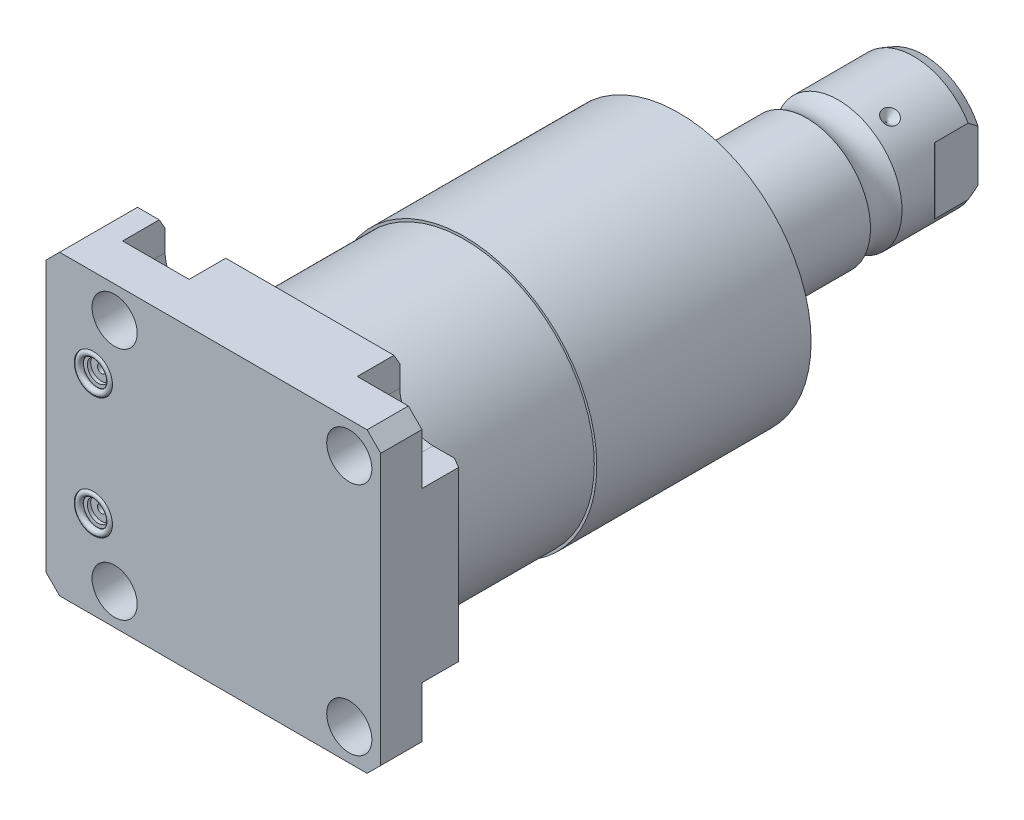
SolidWorks part; units mm, degrees
material "Alloy Steel"
ref_plane "Front Plane" through (0, 0, 0) normal (0, 0, 1) x (1, 0, 0)
ref_plane "Top Plane" through (0, 0, 0) normal (0, 1, 0) x (1, 0, 0)
ref_plane "Right Plane" through (0, 0, 0) normal (1, 0, 0) x (0, 0, -1)
sketch "Sketch1" plane through (0, 0, 0) normal (0, 0, 1) x (1, 0, 0)
  line L0 (-55.55, 44.45) -> (44.45, 44.45)
  line L1 (44.45, 44.45) -> (44.45, -44.45)
  line L2 (44.45, -44.45) -> (-55.55, -44.45)
  line L3 (-55.55, -44.45) -> (-55.55, 44.45)
  dimension "D1" = 100
  dimension "D2" = 88.9
  dimension "D3" = 44.45
  dimension "D4" = 44.45
extrude "Extrude1" add sketch "Sketch1" along normal blind 25.019
hole_wizard "Hole1" positions "Sketch22" profile "Sketch21" legacy end condition through all
sketch "Sketch22" plane through (0, 0, 0) normal (0, 0, -1) x (-1, 0, 0)
  line L0 (0, 0) -> (42.7441, 0) construction
  line L1 (0, 0.8532) -> (0, 27.5062) construction
  point P0 (-35.052, -35.052)
  point P9 (-35.052, 35.052)
  point P11 (35.052, 35.052)
  point P12 (35.052, -35.052)
  dimension "D1" = 35.052
  dimension "D2" = 35.052
sketch "Sketch21" plane through (35.052, -35.052, 0) normal (1, 0, 0) x (0, 1, 0)
  line L0 (0, 0) -> (0, 25.019)
  line L1 (0, 25.019) -> (6.7435, 25.019)
  line L2 (6.7435, 25.019) -> (6.7435, 0)
  line L3 (6.7435, 0) -> (0, 0)
  line L4 (0, 110) -> (0, -10) construction
  dimension "Diameter" = 13.487
  dimension "Depth" = 25.019
sketch "Sketch3" plane through (0, 0, 0) normal (0, 0, -1) x (-1, 0, 0)
  line L0 (-35.052, -25.1205) -> (-44.45, -25.1205)
  line L1 (-44.45, -44.45) -> (-44.45, -25.1205)
  line L2 (-44.45, 25.1205) -> (-44.45, 44.45)
  line L3 (-44.45, 25.1205) -> (-35.052, 25.1205)
  line L4 (-25.1205, 35.052) -> (-25.1205, 44.45)
  line L5 (-44.45, 44.45) -> (-25.1205, 44.45)
  line L6 (25.1205, 44.45) -> (25.1205, 35.052)
  line L7 (44.9835, 35.052) -> (44.9835, 44.45)
  line L8 (25.1205, 44.45) -> (44.9835, 44.45)
  line L9 (44.9835, -44.45) -> (25.1205, -44.45)
  line L10 (44.9835, -44.45) -> (44.9835, -35.052)
  line L11 (25.1205, -35.052) -> (25.1205, -44.45)
  line L12 (-25.1205, -44.45) -> (-44.45, -44.45)
  line L13 (-25.1205, -44.45) -> (-25.1205, -35.052)
  line L14 (-44.45, 44.45) -> (55.55, 44.45) construction
  line L15 (-44.45, -44.45) -> (-44.45, 44.45) construction
  line L16 (55.55, -44.45) -> (-44.45, -44.45) construction
  arc A0 (-25.1205, -35.052) -> (-35.052, -25.1205) centre (-35.052, -35.052) ccw
  arc A1 (-35.052, 25.1205) -> (-25.1205, 35.052) centre (-35.052, 35.052) ccw
  arc A2 (25.1205, 35.052) -> (44.9835, 35.052) centre (35.052, 35.052) ccw
  arc A3 (44.9835, -35.052) -> (25.1205, -35.052) centre (35.052, -35.052) ccw
  circle A8 centre (-35.052, 35.052) radius 6.7435 construction
  circle A9 centre (-35.052, -35.052) radius 6.7435 construction
  circle A10 centre (35.052, -35.052) radius 6.7435 construction
  circle A11 centre (35.052, 35.052) radius 6.7435 construction
  dimension "D1" = 9.9315
extrude "Cut-Extrude2" cut sketch "Sketch3" against normal blind 12.7
ref_plane "Plane16" through (0, 0, 12.014) normal (0, 0, 1) x (1, 0, 0)
sketch "Sketch23" plane through (0, 0, 12.014) normal (0, 0, 1) x (1, 0, 0)
  line L0 (-11.9397, -13.0048) -> (-61.0013, -13.0048) construction
  line L1 (-55.55, -23.749) -> (-55.296, -23.749)
  line L3 (-55.296, -23.749) -> (-55.296, -19.6596)
  line L4 (-55.296, -19.6596) -> (-54.5848, -18.9484)
  line L5 (-54.5848, -18.9484) -> (-41.1228, -18.9484)
  line L6 (-41.1228, -18.9484) -> (-41.1228, -13.0048)
  line L7 (-41.1228, -13.0048) -> (-55.55, -13.0048)
  line L8 (-55.55, -13.0048) -> (-55.55, -23.749)
  line L10 (-55.55, 44.45) -> (-55.55, -44.45) construction
  dimension "D1" = 21.4884
  dimension "D2" = 0.254
  dimension "D3" = 45
  dimension "D4" = 13.3096
  dimension "D5" = 11.8872
  dimension "D6" = 14.1732
  dimension "D7" = 13.0048
revolve "Cut-Revolve5" cut sketch "Sketch23" angle 360 about L0
mirror "Mirror1" about plane through (0, 0, 0) normal (0, 1, 0) of "Cut-Revolve5"
sketch "Sketch6" plane through (0, 0, 25.019) normal (0, 0, 1) x (1, 0, 0)
  line L0 (0, 0) -> (-71.0417, 0) construction
  circle A0 centre (-41.402, -18.11) radius 5.7023
  circle A1 centre (-41.402, 18.11) radius 5.7023
  dimension "D4" = 11.4046
  dimension "D1" = 18.11
  dimension "D2" = 36.22
  dimension "D3" = 41.402
extrude "Cut-Extrude3" cut sketch "Sketch6" against normal blind 1.4478
sketch "Sketch7" plane through (0, 0, 23.5712) normal (0, 0, 1) x (1, 0, 0)
  circle A0 centre (-41.402, 18.11) radius 3.2512
  circle A1 centre (-41.402, -18.11) radius 3.2512
  circle A2 centre (-41.402, 18.11) radius 5.7023 construction
  circle A3 centre (-41.402, -18.11) radius 5.7023 construction
  dimension "D1" = 6.5024
extrude "Cut-Extrude4" cut sketch "Sketch7" against normal blind 1.016
sketch "Sketch8" plane through (0, 0, 22.5552) normal (0, 0, 1) x (1, 0, 0)
  circle A0 centre (-41.402, 18.11) radius 1.2446
  circle A1 centre (-41.402, -18.11) radius 1.2446
  circle A2 centre (-41.402, 18.11) radius 5.7023 construction
  circle A3 centre (-41.402, -18.11) radius 5.7023 construction
  dimension "D1" = 2.4892
extrude "Cut-Extrude5" cut sketch "Sketch8" against normal blind 11.9888
ref_plane "Plane17" through (0, 18.11, 0) normal (0, 1, 0) x (-1, 0, 0)
sketch "Sketch9" plane through (-41.656, 18.11, 23.5712) normal (0, 1, 0) x (1, 0, 0)
  line L0 (0.254, -1.9469) -> (0.254, 0.0927) construction
  line L3 (-5.4483, 0) -> (5.9563, 0) construction
  line L4 (0.254, 13.0048) -> (0.254, 1.016) construction
  circle A0 centre (5.0292, -0.9271) radius 0.9271
  dimension "D1" = 1.8542
  dimension "D2" = 9.5504
revolve "Revolve1" add sketch "Sketch9" angle 360 about L0
mirror "Mirror2" about plane through (0, 0, 0) normal (0, 1, 0) of bodies 116
chamfer "Chamfer1" distance 4.064 angle 45 4 edges at (44.45, -44.45, 18.8595) (44.45, 44.45, 18.8595) (-55.55, 44.45, 12.5095) (-55.55, -44.45, 12.5095)
chamfer "Chamfer2" distance 3.0226 angle 30 5 edges at (-48.2347, -44.45, 0) (0, -44.45, 0) (44.45, 0, 0) (-48.2347, 44.45, 0) (0, 44.45, 0)
sketch "Sketch24" plane through (0, 0, 0) normal (1, 0, 0) x (0, 0, -1)
  line L0 (0, 0) -> (113.9127, 0) construction
  line L1 (0, 0) -> (0, 38.786)
  line L2 (0, 38.786) -> (44.45, 38.786)
  line L3 (44.45, 38.786) -> (44.45, 39.5225)
  line L4 (44.45, 39.5225) -> (108.4839, 39.5225)
  line L5 (108.4839, 39.5225) -> (112.268, 25.4)
  line L6 (112.268, 25.4) -> (112.268, 0)
  line L7 (112.268, 0) -> (0, 0)
  dimension "D1" = 77.572
  dimension "D2" = 44.45
  dimension "D3" = 79.045
  dimension "D4" = 50.8
  dimension "D5" = 15
  dimension "D6" = 112.268
revolve "Revolve4" add sketch "Sketch24" angle 360 about L0
sketch "Sketch17" plane through (0, 0, 0) normal (1, 0, 0) x (0, 0, -1)
  line L0 (112.268, 0) -> (112.268, -19.05)
  line L1 (112.268, -19.05) -> (146.7029, -19.05)
  line L2 (156.1171, -19.05) -> (178.664, -19.05)
  line L3 (181.585, -17.9868) -> (181.585, 0)
  line L4 (181.585, 0) -> (112.268, 0)
  line L5 (130.8989, 0) -> (0.816, 0) construction
  line L6 (112.268, -25.4) -> (112.268, 25.4) construction
  line L7 (-25.019, -40.386) -> (-25.019, 40.386) construction
  line L8 (181.585, -17.9868) -> (178.664, -19.05)
  arc A0 (156.1171, -19.05) -> (146.7029, -19.05) centre (151.41, -25.4254) ccw
  dimension "D2" = 20
  dimension "D4" = 7.9248
  dimension "D5" = 35.0012
  dimension "D1" = 206.604
  dimension "D3" = 38.1
  dimension "D6" = 30.175
  dimension "D7" = 2.921
revolve "Revolve3" add sketch "Sketch17" angle 360 about L5
sketch "Sketch28" plane through (0, 0, 0) normal (0, 1, 0) x (1, 0, 0)
  line L0 (-34.3062, 162.078) -> (35.4095, 162.078) construction
  line L1 (-19.05, 164.491) -> (-16.637, 162.078)
  line L2 (-19.05, 178.664) -> (-19.05, 156.1171) construction
  line L3 (-16.637, 162.078) -> (-19.05, 162.078)
  line L4 (-19.05, 162.078) -> (-19.05, 164.491)
  arc A0 (-19.05, 146.7029) -> (-19.05, 156.1171) centre (-25.4254, 151.41) ccw construction
  dimension "D3" = 10.668
  dimension "D1" = 45
  dimension "D2" = 4.826
revolve "Cut-Revolve6" cut sketch "Sketch28" angle 360 about L0
pattern_circular "CirPattern1" count 3 over 360 about axis through (0, 0, -130.8989) along (0, 0, -1) of "Cut-Revolve6"
hole_wizard "Hole2" positions "Sketch33" profile "Sketch32" legacy
sketch "Sketch33" plane through (0, 0, -181.585) normal (0, 0, -1) x (-1, 0, 0)
  circle A0 centre (0, 0) radius 19.05 construction
  point P0 (0, 0)
sketch "Sketch32" plane through (0, 0, -181.585) normal (1, 0, 0) x (0, 1, 0)
  line L0 (0, 0) -> (0, 29.5665)
  line L1 (0, 29.5665) -> (6.9342, 25.4)
  line L2 (6.9342, 25.4) -> (6.9342, 0)
  line L4 (6.9342, 0) -> (0, 0)
  line L6 (0, 29.5665) -> (-6.9342, 25.4) construction
  line L7 (0, -4.2442) -> (0, 117.3081) construction
  dimension "Diameter" = 13.8684
  dimension "Depth" = 25.4
  dimension "Drill Angle" = 118
sketch "Sketch34" plane through (0, 0, 0) normal (0, 1, 0) x (0, 0, -1)
  line L0 (0, 0) -> (211.3651, 0) construction
  line L1 (165.8009, 19.05) -> (168.3462, 16.5047)
  line L3 (168.885, 16.2815) -> (181.585, 16.2815)
  line L4 (181.585, -17.9868) -> (181.585, 17.9868) construction
  line L5 (181.585, 16.2815) -> (181.585, 19.05)
  line L6 (181.585, 19.05) -> (165.8009, 19.05)
  line L7 (181.585, -19.05) -> (165.8009, -19.05)
  line L8 (181.585, -16.2815) -> (181.585, -19.05)
  line L9 (168.885, -16.2815) -> (181.585, -16.2815)
  line L10 (165.8009, -19.05) -> (168.3462, -16.5047)
  line L11 (178.664, 19.05) -> (164.491, 19.05) construction
  arc A0 (168.885, 16.2815) -> (168.3462, 16.5047) centre (168.885, 17.0435) cw
  arc A1 (168.885, -16.2815) -> (168.3462, -16.5047) centre (168.885, -17.0435) ccw
  dimension "D2" = 0.762
  dimension "D1" = 45
  dimension "D3" = 12.7
  dimension "D4" = 32.563
extrude "Cut-Extrude8" cut sketch "Sketch34" against normal through all and the other way through all
